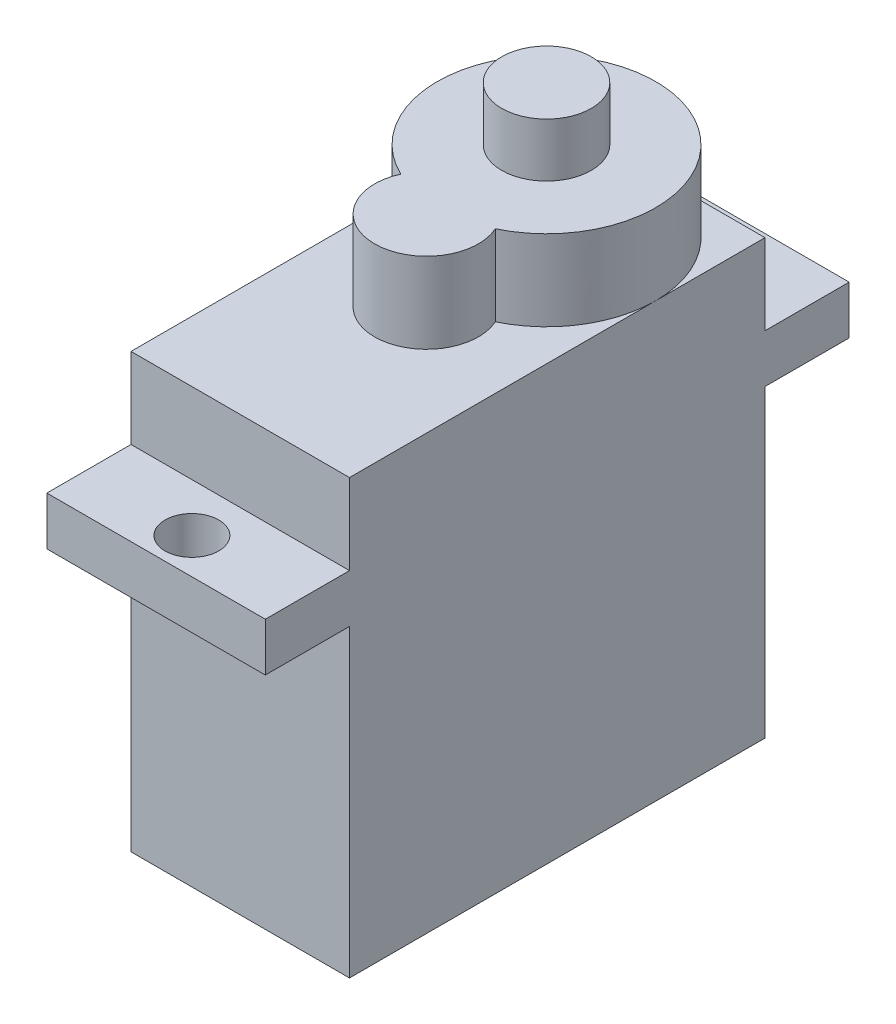
SolidWorks part; units mm, degrees
material "PVC 0.007 Plasticized"
ref_plane "Front Plane" through (0, 0, 0) normal (0, 0, 1) x (1, 0, 0)
ref_plane "Top Plane" through (0, 0, 0) normal (0, 1, 0) x (1, 0, 0)
ref_plane "Right Plane" through (0, 0, 0) normal (1, 0, 0) x (0, 0, -1)
sketch "Sketch1" plane through (0, 0, 0) normal (0, 1, 0) x (1, 0, 0)
  line L1 (-6.1, -11.6) -> (6.1, -11.6)
  line L2 (-6.1, -11.6) -> (-6.1, 11.6)
  line L3 (-6.1, 11.6) -> (6.1, 11.6)
  line L4 (6.1, -11.6) -> (6.1, 11.6)
  line L5 (-6.1, -11.6) -> (6.1, 11.6) construction
  line L6 (-6.1, 11.6) -> (6.1, -11.6) construction
  point P0 (0, 0)
  dimension "D1" = 23.2
  dimension "D2" = 12.2
extrude "Boss-Extrude3" add sketch "Sketch1" along normal blind 24.2
sketch "Sketch5" plane through (0, 0, 11.6) normal (0, 0, 1) x (1, 0, 0)
  line L0 (0, 24.2) -> (0, 19.7) construction
  line L1 (-6.1, 24.2) -> (6.1, 24.2) construction
  line L2 (-6.1, 19.7) -> (6.1, 19.7)
  line L3 (6.1, 24.2) -> (6.1, 0) construction
  line L4 (-6.1, 19.7) -> (-6.1, 17)
  line L5 (-6.1, 24.2) -> (-6.1, 0) construction
  line L6 (-6.1, 17) -> (6.1, 17)
  line L7 (6.1, 17) -> (6.1, 19.7)
  point P10 (0, 19.7)
  dimension "D1" = 4.5
  dimension "D2" = 2.7
extrude "Boss-Extrude4" add sketch "Sketch5" along normal blind 4.7
sketch "Sketch6" plane through (0, 19.7, 0) normal (0, 1, 0) x (1, 0, 0)
  line L0 (6.1, -16.3) -> (-6.1, -16.3) construction
  line L2 (6.1, -16.3) -> (6.1, -11.6) construction
  circle A0 centre (0, -14.3) radius 1.5
  dimension "D1" = 3
  dimension "D2" = 2
  dimension "D3" = 6.1
extrude "Cut-Extrude4" cut sketch "Sketch6" against normal through all both contours A0
mirror "Mirror3" about plane through (0, 0, 0) normal (0, 0, 1) of "Cut-Extrude4", "Boss-Extrude4"
sketch "Sketch7" plane through (0, 24.2, 0) normal (0, 1, 0) x (1, 0, 0)
  line L0 (6.1, 11.6) -> (-6.1, 11.6) construction
  line L1 (6.1, -11.6) -> (6.1, 11.6) construction
  circle A0 centre (0, 5.5) radius 6.1
  circle A1 centre (0, -1.2) radius 2.9
  dimension "D1" = 12.2
  dimension "D3" = 5.8
  dimension "D2" = 1.2
  dimension "D4" = 6.1
  dimension "D5" = 6.1
extrude "Boss-Extrude5" add sketch "Sketch7" along normal blind 4.5 contours A1 A0 | A0 A1 | A0 A1
sketch "Sketch8" plane through (0, 28.7, 0) normal (0, 1, 0) x (1, 0, 0)
  circle A0 centre (0, 5.5) radius 2.5
  dimension "D1" = 5
extrude "Boss-Extrude6" add sketch "Sketch8" along normal blind 3
